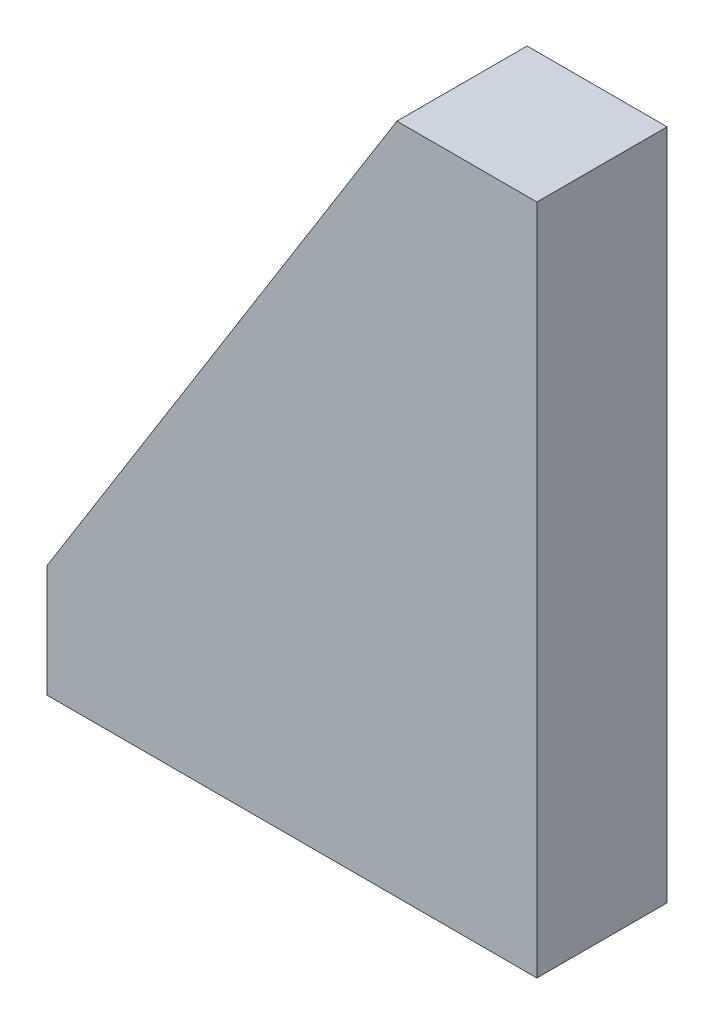
SolidWorks part; units mm, degrees
ref_plane "Front Plane" through (0, 0, 0) normal (0, 0, 1) x (1, 0, 0)
ref_plane "Top Plane" through (0, 0, 0) normal (0, 1, 0) x (1, 0, 0)
ref_plane "Right Plane" through (0, 0, 0) normal (1, 0, 0) x (0, 0, -1)
sketch "Sketch1" plane through (0, 0, 0) normal (0, 0, 1) x (1, 0, 0)
  line L0 (0, 0) -> (0, 42)
  line L1 (0, 42) -> (-10, 42)
  line L2 (-10, 42) -> (-35, 2)
  line L3 (-35, 2) -> (-35, 0)
  line L4 (-35, 0) -> (0, 0)
  dimension "D1" = 42
  dimension "D2" = 35
  dimension "D3" = 2
  dimension "D4" = 10
extrude "Boss-Extrude1" add sketch "Sketch1" against normal blind 9.3
sketch "Sketch2" plane through (0, 0, 0) normal (0, 0, 1) x (1, 0, 0)
  line L0 (-35, 0) -> (0, 0)
  line L1 (0, 0) -> (0, -6)
  line L2 (0, -6) -> (-35, -6)
  line L3 (-35, -6) -> (-35, 0)
  dimension "D1" = 6
extrude "Boss-Extrude2" add sketch "Sketch2" against normal up to surface (9.3 mm away) up to face at (-16, 17.2, -9.3)
